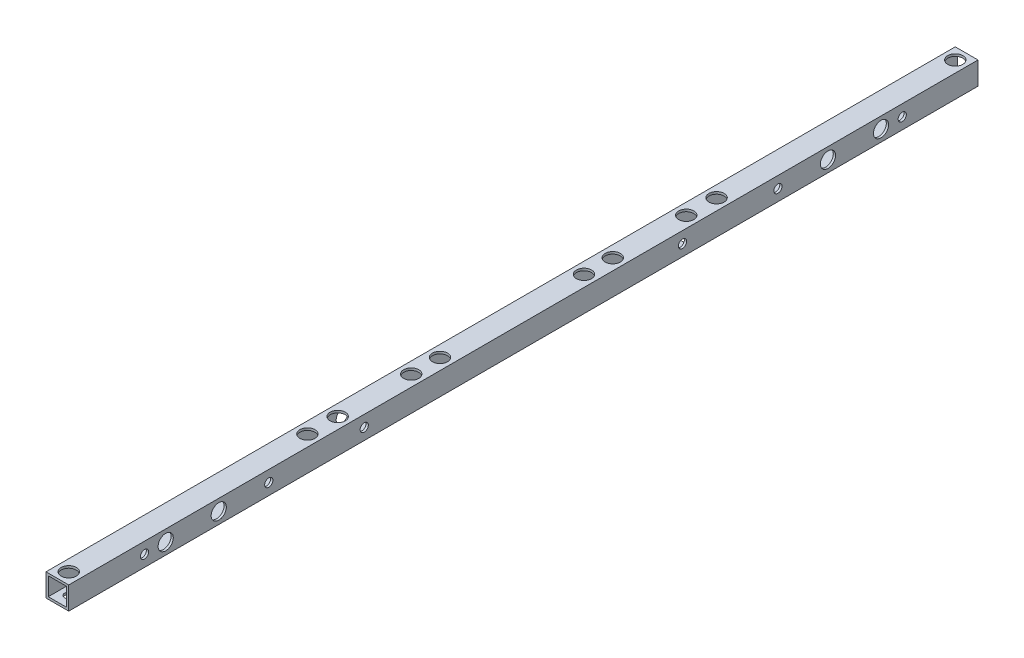
SolidWorks part; units mm, degrees
material "6063-T5"
ref_plane "正面" through (0, 0, 0) normal (0, 0, 1) x (1, 0, 0)
ref_plane "平面" through (0, 0, 0) normal (0, 1, 0) x (1, 0, 0)
ref_plane "右側面" through (0, 0, 0) normal (1, 0, 0) x (0, 0, -1)
sketch "ｽｹｯﾁ1" plane through (0, 0, 0) normal (0, 0, 1) x (1, 0, 0)
  line L1 (-7.5, -7.5) -> (7.5, -7.5)
  line L2 (-7.5, -7.5) -> (-7.5, 7.5)
  line L3 (-7.5, 7.5) -> (7.5, 7.5)
  line L4 (7.5, -7.5) -> (7.5, 7.5)
  line L5 (-7.5, -7.5) -> (7.5, 7.5) construction
  line L6 (-7.5, 7.5) -> (7.5, -7.5) construction
  line L7 (-6, -6) -> (6, -6)
  line L8 (-6, -6) -> (-6, 6)
  line L9 (-6, 6) -> (6, 6)
  line L10 (6, -6) -> (6, 6)
  line L11 (-6, -6) -> (6, 6) construction
  line L12 (-6, 6) -> (6, -6) construction
  point P0 (0, 0)
  point P6 (0, 0)
  dimension "D1" = 1.5
  dimension "D2" = 15
  dimension "D3" = 15
extrude "ﾎﾞｽ - 押し出し1" add sketch "ｽｹｯﾁ1" along normal blind 600
sketch "ｽｹｯﾁ3" plane through (0, 7.5, 0) normal (0, 1, 0) x (1, 0, 0)
  line L0 (-7.5, -600) -> (-7.5, 0) construction
  line L2 (7.5, -600) -> (7.5, 0) construction
  line L3 (7.5, 0) -> (-7.5, 0) construction
  circle A1 centre (0, -7.5) radius 2.7
  circle A6 centre (0, -592.5) radius 2.7
  circle A7 centre (0, -366.5) radius 2.7
  circle A8 centre (0, -233.5) radius 2.7
  point P10 (-7.5, -300)
  dimension "D2" = 7.5
  dimension "D3" = 5.4
  dimension "D7" = 66.5
  dimension "D8" = 2
  dimension "D9" = 7.5
  dimension "D11" = 7.5
  dimension "D4" = 7.5
  dimension "D5" = 5.4
  dimension "D10" = 133
  dimension "D6" = 2
extrude "ｶｯﾄ - 押し出し2" cut sketch "ｽｹｯﾁ3" against normal blind 25
sketch "ｽｹｯﾁ4" plane through (7.5, 0, 0) normal (1, 0, 0) x (0, 0, -1)
  line L0 (-600, -7.5) -> (-600, 7.5) construction
  line L1 (-600, -7.5) -> (0, -7.5) construction
  line L2 (0, -7.5) -> (0, 7.5) construction
  line L3 (-300, 7.5) -> (-300, -7.5) construction
  line L4 (-600, 7.5) -> (0, 7.5) construction
  circle A0 centre (-536, 0) radius 2.7
  circle A1 centre (-501, 0) radius 2.7
  circle A2 centre (-99, 0) radius 2.7
  circle A3 centre (-64, 0) radius 2.7
  circle A7 centre (-132, 0) radius 2.7
  circle A10 centre (-195, 0) radius 2.7
  circle A11 centre (-50, 0) radius 2.7
  circle A12 centre (-550, 0) radius 2.7
  circle A13 centre (-405, 0) radius 2.7
  circle A14 centre (-468, 0) radius 2.7
  dimension "D2" = 7.5
  dimension "D3" = 5.4
  dimension "D5" = 35
  dimension "D7" = 64
  dimension "D9" = 145
  dimension "D13" = 132
  dimension "D8" = 63
  dimension "D10" = 5.4
  dimension "D1" = 64
  dimension "D4" = 2
  dimension "D6" = 2
extrude "ｶｯﾄ - 押し出し3" cut sketch "ｽｹｯﾁ4" against normal blind 20
sketch "ｽｹｯﾁ6" plane through (0, 7.5, 0) normal (0, 1, 0) x (1, 0, 0)
  line L0 (7.5, -600) -> (7.5, 0) construction
  line L1 (7.5, -600) -> (-7.5, -600) construction
  line L2 (7.5, 0) -> (-7.5, 0) construction
  circle A0 centre (0, -435) radius 2.75
  circle A1 centre (0, -415) radius 2.75
  circle A2 centre (0, -165) radius 2.75
  circle A3 centre (0, -185) radius 2.75
  dimension "D1" = 5.5
  dimension "D2" = 7.5
  dimension "D3" = 165
  dimension "D5" = 20
  dimension "D7" = 165
  dimension "D4" = 2
  dimension "D6" = 2
extrude "ｶｯﾄ - 押し出し5" cut sketch "ｽｹｯﾁ6" against normal blind 30
sketch "ｽｹｯﾁ7" plane through (0, 7.5, 0) normal (0, 1, 0) x (1, 0, 0)
  circle A0 centre (0, -7.5) radius 5
  circle A3 centre (0, -165) radius 5
  circle A4 centre (0, -185) radius 5
  circle A5 centre (0, -233.5) radius 5
  circle A6 centre (0, -366.5) radius 5
  circle A7 centre (0, -415) radius 5
  circle A8 centre (0, -435) radius 5
  circle A11 centre (0, -592.5) radius 5
  dimension "D1" = 10
  dimension "D4" = 10
  dimension "D5" = 10
  dimension "D6" = 10
  dimension "D7" = 10
  dimension "D8" = 10
  dimension "D9" = 10
  dimension "D10" = 10
extrude "ｶｯﾄ - 押し出し6" cut sketch "ｽｹｯﾁ7" against normal blind 10
sketch "ｽｹｯﾁ8" plane through (7.5, 0, 0) normal (1, 0, 0) x (0, 0, -1)
  circle A0 centre (-64, 0) radius 5
  circle A1 centre (-99, 0) radius 5
  circle A4 centre (-501, 0) radius 5
  circle A5 centre (-536, 0) radius 5
  dimension "D1" = 10
  dimension "D2" = 10
  dimension "D4" = 10
  dimension "D5" = 10
extrude "ｶｯﾄ - 押し出し7" cut sketch "ｽｹｯﾁ8" against normal blind 10
sketch "ｽｹｯﾁ9" plane through (-7.5, 0, 0) normal (-1, 0, 0) x (0, 0, 1)
  circle A0 centre (132, 0) radius 5
  circle A2 centre (50, 0) radius 5
  circle A3 centre (195, 0) radius 5
  circle A4 centre (405, 0) radius 5
  circle A5 centre (550, 0) radius 5
  circle A6 centre (468, 0) radius 5
  dimension "D3" = 10
extrude "ｶｯﾄ - 押し出し8" cut sketch "ｽｹｯﾁ9" against normal blind 10
hole_wizard "Ø5.4 (5.4) 直径の穴1" positions "ｽｹｯﾁ12" profile "ｽｹｯﾁ13" hole size "Ø5.4" standard "JIS" end condition through all
sketch "ｽｹｯﾁ12" plane through (0, -7.5, 0) normal (0, -1, 0) x (-1, 0, 0)
  line L0 (-7.5, -600) -> (-7.5, 0) construction
  point P0 (0, -252.5)
  point P2 (0, -347.5)
  point P7 (-7.5, -300)
  dimension "D1" = 95
  dimension "D2" = 47.5
sketch "ｽｹｯﾁ13" plane through (0, -7.5, 252.5) normal (1, 0, 0) x (0, 0, -1)
  line L0 (0, 0) -> (0, 15)
  line L1 (0, 15) -> (2.7, 15)
  line L2 (2.7, 15) -> (2.7, 0)
  line L5 (2.7, 0) -> (0, 0)
  line L11 (0, -6.35) -> (0, 107.95) construction
  dimension "通し穴の直径" = 5.4
  dimension "通し穴の深さ" = 15
sketch "ｽｹｯﾁ15" plane through (0, 7.5, 0) normal (0, 1, 0) x (1, 0, 0)
  circle A0 centre (0, -252.5) radius 5
  circle A1 centre (0, -347.5) radius 5
  dimension "D1" = 10
extrude "ｶｯﾄ - 押し出し9" cut sketch "ｽｹｯﾁ15" against normal up to next
equation "\"D2@ｽｹｯﾁ12\"= \"D1@ｽｹｯﾁ12\" / 2"
